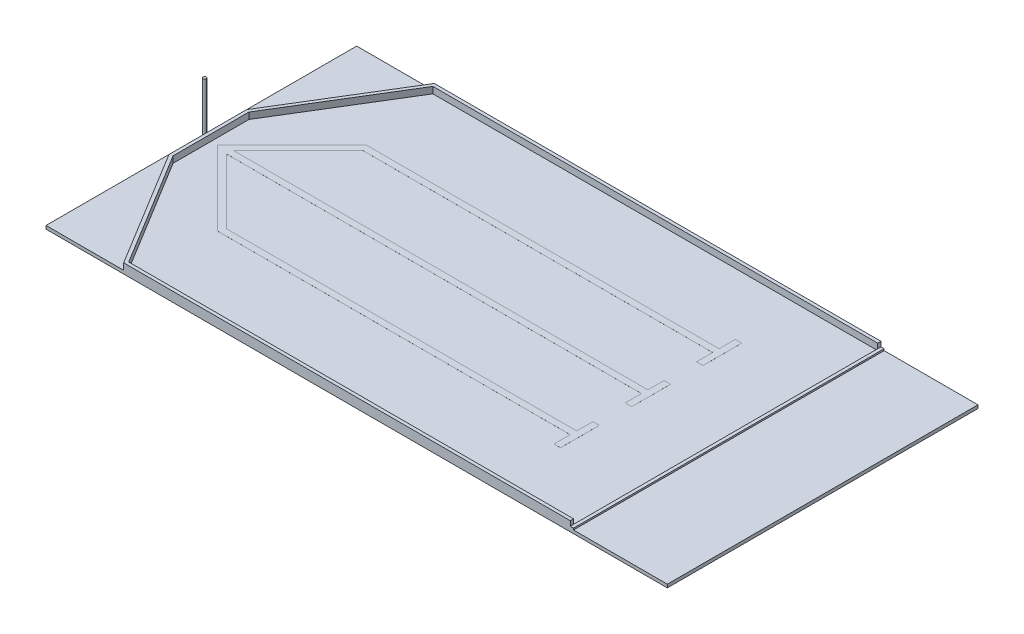
SolidWorks part; units mm, degrees
ref_plane "Front Plane" through (0, 0, 0) normal (0, 0, 1) x (1, 0, 0)
ref_plane "Top Plane" through (0, 0, 0) normal (0, 1, 0) x (1, 0, 0)
ref_plane "Right Plane" through (0, 0, 0) normal (1, 0, 0) x (0, 0, -1)
sketch "Sketch1" plane through (0, 0, 0) normal (0, 1, 0) x (1, 0, 0)
  line L1 (0, 0) -> (2438.4, 0)
  line L2 (0, 0) -> (0, -1219.2)
  line L3 (0, -1219.2) -> (2438.4, -1219.2)
  line L4 (2438.4, 0) -> (2438.4, -1219.2)
  dimension "D1" = 2438.4
  dimension "D2" = 1219.2
extrude "Base" add sketch "Sketch1" along normal blind 12.7
sketch "Sketch2" plane through (0, 12.7, 0) normal (0, 1, 0) x (1, 0, 0)
  line L0 (304.8, 0) -> (25.4, -457.2)
  line L1 (2438.4, 0) -> (0, 0) construction
  line L2 (25.4, -457.2) -> (25.4, -762)
  line L3 (25.4, -762) -> (304.8, -1219.2)
  line L4 (0, -1219.2) -> (2438.4, -1219.2) construction
  line L5 (304.8, -1219.2) -> (2057.4, -1219.2)
  line L6 (304.8, 0) -> (2057.4, 0)
  line L7 (0, 0) -> (0, -1219.2) construction
  line L8 (2438.4, -1219.2) -> (2438.4, 0) construction
  line L9 (0, -609.6) -> (2438.4, -609.6) construction
  line L10 (311.9226, -12.7) -> (2057.4, -12.7)
  line L11 (311.9226, -12.7) -> (38.1, -460.7733)
  line L12 (38.1, -460.7733) -> (38.1, -758.4267)
  line L13 (38.1, -758.4267) -> (311.9226, -1206.5)
  line L14 (311.9226, -1206.5) -> (2057.4, -1206.5)
  line L15 (2057.4, 0) -> (2057.4, -12.7)
  line L16 (2057.4, -1206.5) -> (2057.4, -1219.2)
  point P16 (25.4, -609.6)
  dimension "D1" = 304.8
  dimension "D2" = 304.8
  dimension "D3" = 25.4
  dimension "D4" = 381
  dimension "D5" = 12.7
extrude "Outside Walls" add sketch "Sketch2" along normal blind 25.4
sketch "Sketch3" plane through (0, 12.7, 0) normal (0, 1, 0) x (1, 0, 0)
  line L0 (2057.4, 0) -> (2057.4, -1219.2)
  line L1 (2057.4, -1219.2) -> (2070.1, -1219.2)
  line L2 (2057.4, -1219.2) -> (2438.4, -1219.2) construction
  line L3 (2070.1, -1219.2) -> (2070.1, 0)
  line L4 (2438.4, 0) -> (2057.4, 0) construction
  line L5 (2070.1, 0) -> (2057.4, 0)
  dimension "D1" = 12.7
extrude "Front Wall" add sketch "Sketch3" along normal blind 6.35
sketch "Sketch4" plane through (0, 12.7, 0) normal (0, 1, 0) x (1, 0, 0)
  line L0 (63.5, -609.6) -> (2438.4, -609.6) construction
  line L2 (2438.4, -1219.2) -> (2438.4, 0) construction
  line L3 (63.5, -609.6) -> (1752.6, -609.6) construction
  line L4 (63.5, -609.6) -> (355.6, -317.5)
  line L5 (355.6, -317.5) -> (1752.6, -317.5)
  line L6 (63.5, -609.6) -> (355.6, -901.7)
  line L7 (355.6, -901.7) -> (1752.6, -901.7)
  line L8 (2057.4, -1206.5) -> (311.9226, -1206.5) construction
  line L9 (311.9226, -12.7) -> (2057.4, -12.7) construction
  line L10 (38.1, -758.4267) -> (38.1, -460.7733) construction
  line L11 (1752.6, -254) -> (1752.6, -406.4) construction
  line L12 (1752.6, -533.4) -> (1752.6, -685.8) construction
  line L13 (1752.6, -812.8) -> (1752.6, -965.2) construction
  line L14 (2057.4, -12.7) -> (2057.4, -1206.5) construction
  line L15 (76.2, -622.3) -> (1752.6, -622.3)
  line L16 (72.4803, -618.5803) -> (360.8605, -330.2) construction
  line L17 (360.8605, -330.2) -> (1752.6, -330.2) construction
  line L18 (63.5, -622.3) -> (1752.6, -622.3) construction
  line L19 (63.5, -596.9) -> (1752.6, -596.9) construction
  line L20 (1739.9, -254) -> (1739.9, -406.4)
  line L21 (1739.9, -533.4) -> (1739.9, -685.8)
  line L22 (1739.9, -812.8) -> (1739.9, -965.2)
  line L23 (76.2, -596.9) -> (1752.6, -596.9)
  line L24 (72.4803, -636.5408) -> (54.5197, -618.5803)
  line L25 (72.4803, -636.5408) -> (366.121, -342.9)
  line L26 (72.4803, -600.6197) -> (360.8605, -889) construction
  line L27 (360.8605, -889) -> (1752.6, -889) construction
  line L28 (1765.3, -254) -> (1765.3, -406.4)
  line L29 (1765.3, -533.4) -> (1765.3, -685.8)
  line L30 (1765.3, -812.8) -> (1765.3, -965.2)
  line L31 (366.121, -342.9) -> (1752.6, -342.9)
  line L32 (1752.6, -622.3) -> (1752.6, -596.9)
  line L33 (72.4803, -618.5803) -> (63.5, -609.6) construction
  line L34 (72.4803, -618.5803) -> (72.4803, -618.5803)
  line L35 (63.5, -609.6) -> (72.4803, -600.6197) construction
  line L36 (72.4803, -618.5803) -> (355.6, -901.7)
  line L37 (1739.9, -254) -> (1765.3, -254)
  line L38 (1739.9, -406.4) -> (1765.3, -406.4)
  line L39 (1739.9, -533.4) -> (1765.3, -533.4)
  line L40 (1739.9, -685.8) -> (1765.3, -685.8)
  line L41 (1739.9, -812.8) -> (1765.3, -812.8)
  line L42 (1739.9, -965.2) -> (1765.3, -965.2)
  line L43 (355.6, -901.7) -> (1752.6, -901.7)
  line L44 (81.4605, -591.6395) -> (369.8408, -880.0197)
  line L45 (360.8605, -876.3) -> (1752.6, -876.3)
  dimension "D1" = 45
  dimension "D2" = 45
  dimension "D3" = 304.8
  dimension "D4" = 304.8
  dimension "D5" = 25.4
  dimension "D6" = 152.4
  dimension "D7" = 152.4
  dimension "D8" = 152.4
  dimension "D9" = 304.8
  dimension "D10" = 12.7
  dimension "D11" = 12.7
  dimension "D12" = 12.7
  dimension "D13" = 12.7
  dimension "D14" = 12.7
extrude "Tape" add sketch "Sketch4" along normal blind 0.1
sketch "Sketch5" plane through (0, 12.7, 0) normal (0, 1, 0) x (1, 0, 0)
  line L0 (0, 0) -> (0, -1219.2) construction
  circle A0 centre (12.7, -609.6) radius 6.35
  dimension "D1" = 12.7
  dimension "D2" = 12.7
extrude "10kHz Emitter" add sketch "Sketch5" along normal blind 203.2
